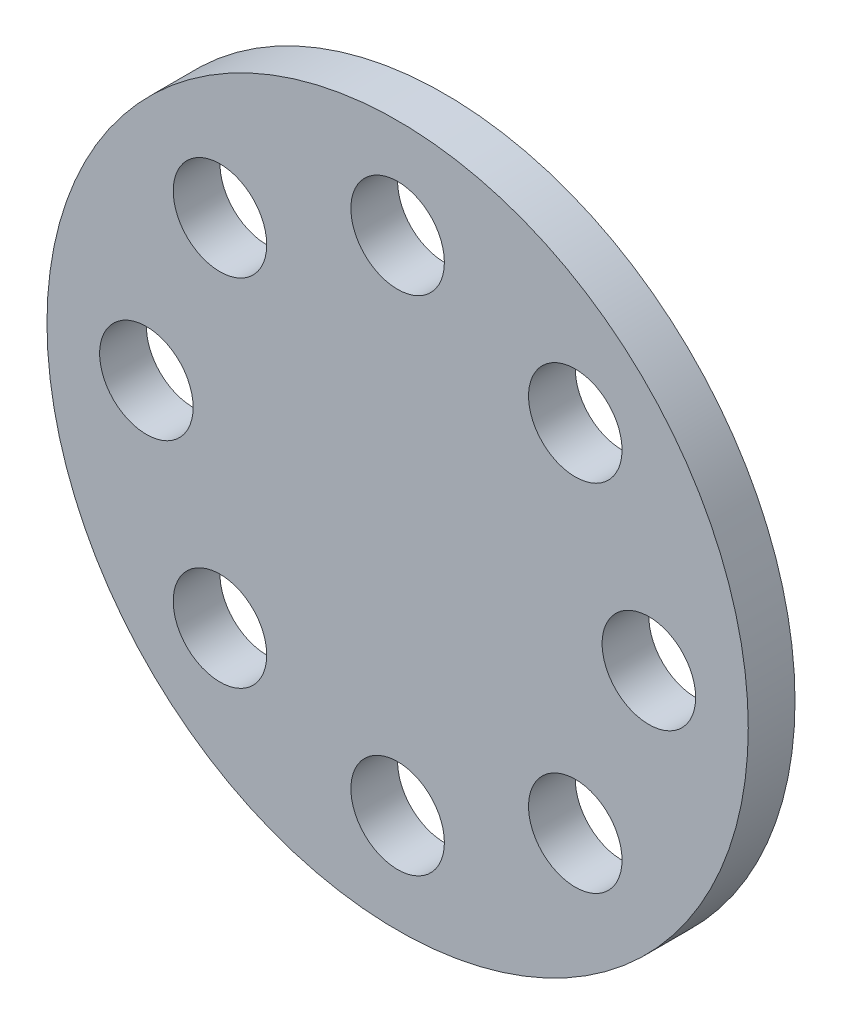
SolidWorks part; units mm, degrees
ref_plane "Front Plane" through (0, 0, 0) normal (0, 0, 1) x (1, 0, 0)
ref_plane "Top Plane" through (0, 0, 0) normal (0, 1, 0) x (1, 0, 0)
ref_plane "Right Plane" through (0, 0, 0) normal (1, 0, 0) x (0, 0, -1)
sketch "Sketch1" plane through (0, 0, 0) normal (0, 0, 1) x (1, 0, 0)
  line L0 (0, 0) -> (0, 28.3981) construction
  circle A0 centre (0, 0) radius 75
  circle A1 centre (0, 53.7379) radius 10
  circle A2 centre (37.9984, 37.9984) radius 10
  circle A3 centre (53.7379, 0) radius 10
  circle A4 centre (37.9984, -37.9984) radius 10
  circle A5 centre (0, -53.7379) radius 10
  circle A6 centre (-37.9984, -37.9984) radius 10
  circle A7 centre (-53.7379, 0) radius 10
  circle A8 centre (-37.9984, 37.9984) radius 10
  point P23 (0, 0)
  dimension "D1" = 150
  dimension "D2" = 20
  dimension "D3" = 8
extrude "Boss-Extrude1" add sketch "Sketch1" along normal blind 10
